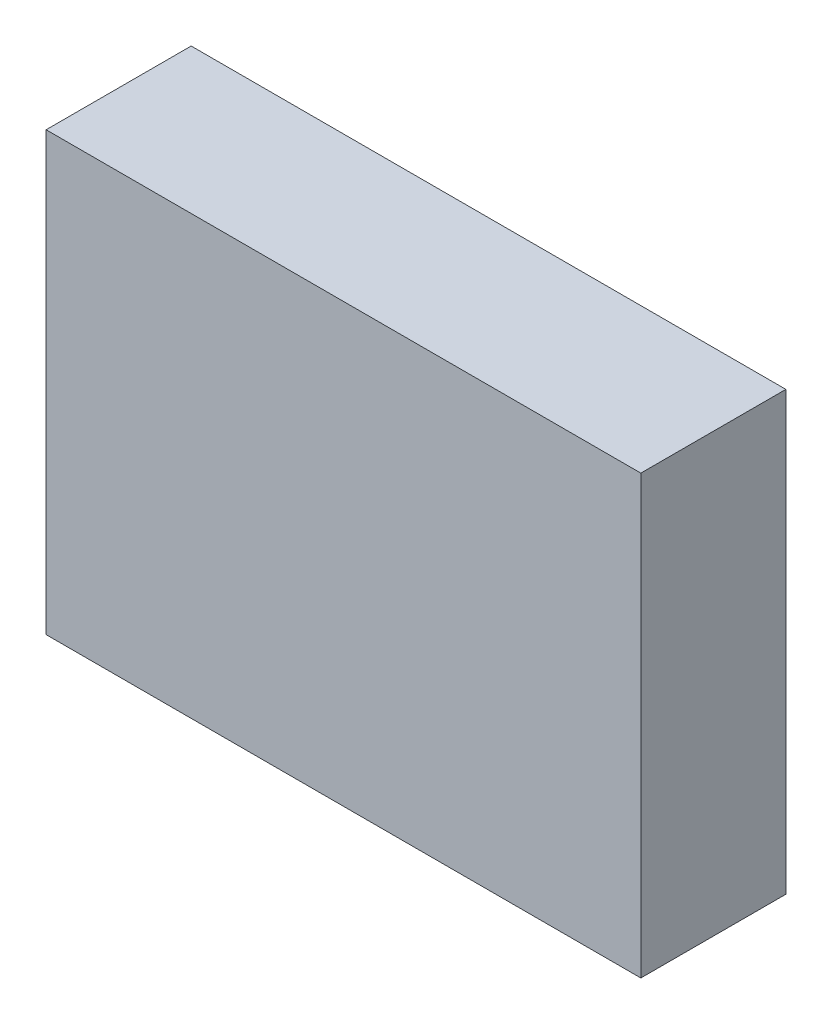
SolidWorks part; units mm, degrees
ref_plane "Front Plane" through (0, 0, 0) normal (0, 0, 1) x (1, 0, 0)
ref_plane "Top Plane" through (0, 0, 0) normal (0, 1, 0) x (1, 0, 0)
ref_plane "Right Plane" through (0, 0, 0) normal (1, 0, 0) x (0, 0, -1)
sketch "Sketch1" plane through (0, 0, 0) normal (0, 0, 1) x (1, 0, 0)
  line L0 (-3.5877, -2.6378) -> (3.5877, -2.6378)
  line L1 (3.5877, -2.6378) -> (3.5877, 2.6378)
  line L2 (3.5877, 2.6378) -> (-3.5877, 2.6378)
  line L3 (-3.5877, 2.6378) -> (-3.5877, -2.6378)
extrude "Component_Outline" add sketch "Sketch1" along normal blind 1.7501 separate body
sketch3d "3DSketch1"
  line L0 (0, 0, 0) -> (1, 0, 0)
  line L1 (0, 0, 0) -> (0, 1, 0)
  line L2 (0, 0, 0) -> (0, 0, 1)
  point P0 (0, 0, 0)
